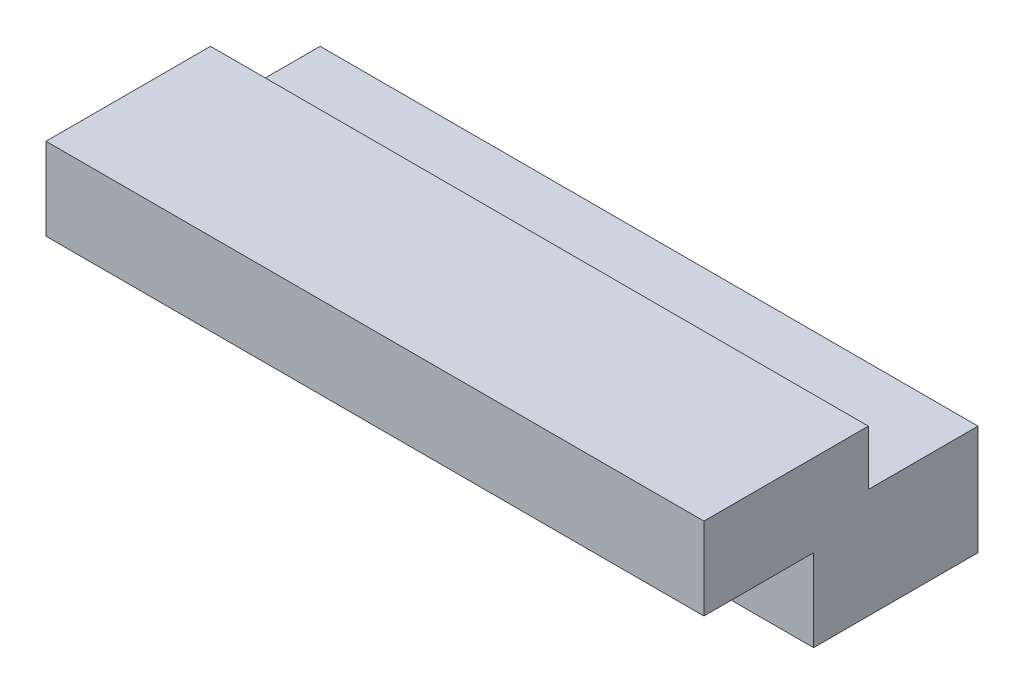
SolidWorks part; units mm, degrees
material "ABS"
ref_plane "前视基准面" through (0, 0, 0) normal (0, 0, 1) x (1, 0, 0)
ref_plane "上视基准面" through (0, 0, 0) normal (0, 1, 0) x (1, 0, 0)
ref_plane "右视基准面" through (0, 0, 0) normal (1, 0, 0) x (0, 0, -1)
sketch "草图3" plane through (0, 0.0878, 0) normal (0, -1, 0) x (1, 0, 0)
  line L0 (-23.3685, 14.324) -> (76.6315, 14.324) construction
  line L1 (56.6315, 4.324) -> (-3.3685, 4.324)
  line L2 (56.6315, 4.324) -> (56.6315, 14.324)
  line L3 (56.6315, 14.324) -> (-3.3685, 14.324)
  line L4 (-3.3685, 4.324) -> (-3.3685, 14.324)
  dimension "D1" = 0
  dimension "D2" = 20
  dimension "D3" = 20
  dimension "D4" = 10
extrude "凸台-拉伸1" add sketch "草图3" along normal blind 10
sketch "草图4" plane through (0, 0, 14.324) normal (0, 0, 1) x (1, 0, 0)
  line L2 (-3.3685, -9.9122) -> (56.6315, -9.9122)
  line L3 (-3.3685, -9.9122) -> (-3.3685, 0.0878)
  line L4 (-3.3685, 0.0878) -> (56.6315, 0.0878)
  line L5 (56.6315, -9.9122) -> (56.6315, 0.0878)
extrude "凸台-拉伸2" add sketch "草图4" along normal blind 5
sketch "草图5" plane through (0, 0.0878, 0) normal (0, 1, 0) x (1, 0, 0)
  line L0 (56.6315, -4.324) -> (56.6315, -19.324) construction
  line L1 (-3.3685, -19.324) -> (56.6315, -19.324)
  line L2 (-3.3685, -19.324) -> (-3.3685, -14.324)
  line L3 (-3.3685, -14.324) -> (56.6315, -14.324)
  line L4 (56.6315, -19.324) -> (56.6315, -14.324)
  line L5 (-23.3685, -14.324) -> (76.6315, -14.324) construction
  dimension "D1" = 0
extrude "凸台-拉伸3" add sketch "草图5" along normal blind 5
sketch "草图6" plane through (0, 0, 19.324) normal (0, 0, 1) x (1, 0, 0)
  line L0 (56.6315, -9.9122) -> (56.6315, 5.0878) construction
  line L1 (-3.3685, 5.0878) -> (56.6315, 5.0878)
  line L2 (-3.3685, 5.0878) -> (-3.3685, -2.4122)
  line L3 (-3.3685, -2.4122) -> (56.6315, -2.4122)
  line L4 (56.6315, 5.0878) -> (56.6315, -2.4122)
  dimension "D1" = 7.5
extrude "凸台-拉伸4" add sketch "草图6" along normal blind 10
